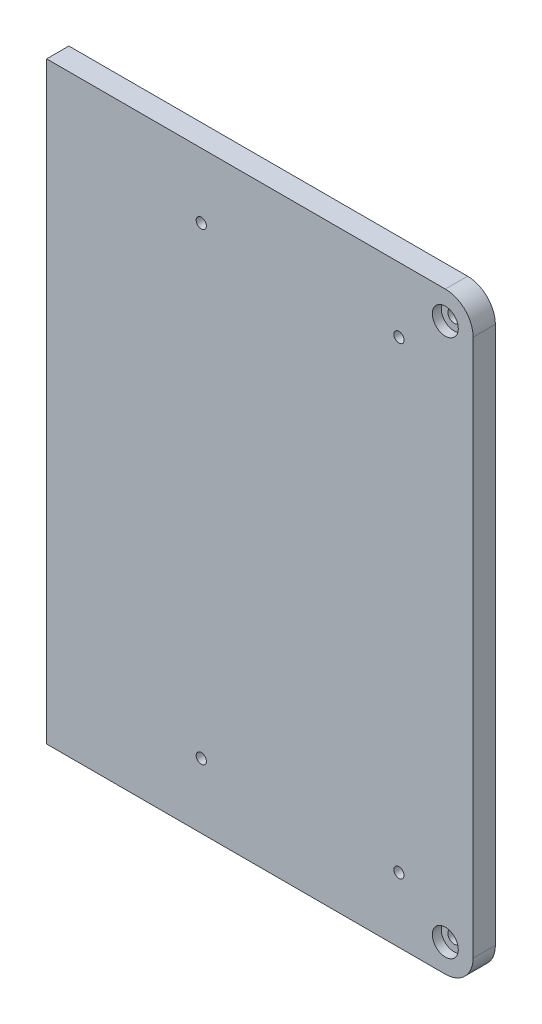
SolidWorks part; units mm, degrees
ref_plane "Front Plane" through (0, 0, 0) normal (0, 0, 1) x (1, 0, 0)
ref_plane "Top Plane" through (0, 0, 0) normal (0, 1, 0) x (1, 0, 0)
ref_plane "Right Plane" through (0, 0, 0) normal (1, 0, 0) x (0, 0, -1)
sketch "Sketch1" plane through (0, 0, 0) normal (0, 0, 1) x (1, 0, 0)
  line L1 (-107.5, 80) -> (107.5, 80)
  line L2 (-115, 72.5) -> (-115, -72.5)
  line L3 (-107.5, -80) -> (107.5, -80)
  line L4 (115, 72.5) -> (115, -72.5)
  line L5 (-115, 80) -> (115, -80) construction
  line L6 (-115, -80) -> (115, 80) construction
  arc A0 (-115, -72.5) -> (-107.5, -80) centre (-107.5, -72.5) ccw
  arc A1 (107.5, -80) -> (115, -72.5) centre (107.5, -72.5) ccw
  arc A2 (107.5, 80) -> (115, 72.5) centre (107.5, 72.5) cw
  arc A3 (-107.5, 80) -> (-115, 72.5) centre (-107.5, 72.5) ccw
  point P0 (0, 0)
  dimension "D3" = 7.5
  dimension "D1" = 230
  dimension "D2" = 160
extrude "Boss-Extrude1" add sketch "Sketch1" along normal blind 6
sketch "Sketch4" plane through (0, 0, 6) normal (0, 0, 1) x (1, 0, 0)
  line L0 (107.5, 80) -> (-107.5, 80) construction
  line L3 (-115, 72.5) -> (-115, -72.5) construction
  line L4 (-107.5, -80) -> (107.5, -80) construction
  circle A0 centre (-96.5, 37.5) radius 1.5
  circle A1 centre (-96.5, -37.5) radius 1.5
  circle A2 centre (-24.5, 37.5) radius 1.5
  circle A3 centre (-24.5, -37.5) radius 1.5
  dimension "D2" = 3
  dimension "D3" = 3
  dimension "D6" = 3
  dimension "D7" = 3
  dimension "D12" = 18.5
  dimension "D1" = 75
  dimension "D4" = 42.5
  dimension "D5" = 18.5
  dimension "D8" = 72
  dimension "D9" = 72
  dimension "D10" = 42.5
  dimension "D11" = 42.5
extrude "Cut-Extrude3" cut sketch "Sketch4" against normal through all
sketch "Sketch5" plane through (0, 0, 6) normal (0, 0, 1) x (1, 0, 0)
  line L0 (-107.5, -80) -> (107.5, -80) construction
  line L1 (107.5, 80) -> (-107.5, 80) construction
  line L2 (115, -72.5) -> (115, 72.5) construction
  circle A0 centre (95, -62.5) radius 1.375
  circle A1 centre (95, 62.5) radius 1.375
  circle A2 centre (41.7, -62.5) radius 1.375
  circle A3 centre (41.7, 62.5) radius 1.375
  dimension "D1" = 125
  dimension "D4" = 2.75
  dimension "D6" = 53.3
  dimension "D7" = 125
  dimension "D8" = 20
  dimension "D9" = 17.5
  dimension "D2" = 17.5
  dimension "D3" = 20
  dimension "D5" = 53.3
extrude "Cut-Extrude4" cut sketch "Sketch5" against normal through all and the other way through all
sketch "Sketch7" plane through (0, 0, 6) normal (0, 0, 1) x (1, 0, 0)
  circle A0 centre (-102.8, 42.3) radius 1.5
  circle A1 centre (-96.5, 37.5) radius 1.5 construction
  circle A2 centre (-102.8, -42.3) radius 1.5
  circle A3 centre (-18.2, -42.3) radius 1.5
  circle A4 centre (-18.2, 42.3) radius 1.5
  circle A5 centre (-96.5, -37.5) radius 1.5 construction
  circle A6 centre (-24.5, -37.5) radius 1.5 construction
  circle A7 centre (-24.5, 37.5) radius 1.5 construction
  dimension "D1" = 6.3
  dimension "D3" = 3
  dimension "D4" = 3
  dimension "D5" = 3
  dimension "D6" = 3
  dimension "D7" = 4.8
  dimension "D8" = 6.3
  dimension "D10" = 4.8
  dimension "D11" = 4.8
  dimension "D12" = 6.3
  dimension "D2" = 4.8
extrude "Cut-Extrude6" cut sketch "Sketch7" against normal through all
sketch "Sketch8" plane through (0, 0, 0) normal (0, 0, -1) x (-1, 0, 0)
  circle A0 centre (18.2, 42.3) radius 3
  circle A1 centre (18.2, -42.3) radius 3
  circle A2 centre (102.8, -42.3) radius 3
  circle A3 centre (102.8, 42.3) radius 3
  dimension "D1" = 6
  dimension "D2" = 6
  dimension "D3" = 6
  dimension "D4" = 6
extrude "Cut-Extrude7" cut sketch "Sketch8" against normal blind 3.5
hole_wizard "CBORE for M3 Pan Head Machine Screw1" positions "Sketch9" profile "Sketch10" counterbore size "M3" standard "ANSI Metric" end condition through all
sketch "Sketch9" plane through (0, 0, 6) normal (0, 0, 1) x (1, 0, 0)
  line L1 (107.5, 80) -> (-107.5, 80) construction
  line L2 (-115, 72.5) -> (-115, -72.5) construction
  line L3 (-107.5, -80) -> (107.5, -80) construction
  line L4 (115, -72.5) -> (115, 72.5) construction
  point P0 (-107.5, 72.5)
  point P2 (-107.5, -72.5)
  point P4 (107.5, -72.5)
  point P6 (107.5, 72.5)
  dimension "D1" = 7.5
  dimension "D2" = 7.5
  dimension "D3" = 7.5
  dimension "D4" = 7.5
  dimension "D5" = 7.5
  dimension "D6" = 7.5
  dimension "D7" = 7.5
  dimension "D8" = 7.5
sketch "Sketch10" plane through (-107.5, 72.5, 6) normal (1, 0, 0) x (0, -1, 0)
  line L0 (0, 0) -> (0, 6)
  line L1 (0, 6) -> (1.7, 6)
  line L3 (1.7, 6) -> (1.7, 2.4)
  line L4 (1.7, 2.4) -> (3.5, 2.4)
  line L5 (3.5, 2.4) -> (3.5, 0)
  line L7 (3.5, 0) -> (0, 0)
  line L11 (0, -6.35) -> (0, 107.95) construction
  dimension "Thru Hole Dia." = 3.4
  dimension "Thru Hole Depth" = 6
  dimension "C'Bore Dia." = 7
  dimension "C'Bore Depth" = 2.4
sketch "Sketch12" plane through (0, 0, 0) normal (0, 0, -1) x (-1, 0, 0)
  line L0 (115, 72.5) -> (115, -72.5) construction
  line L1 (115, 80) -> (0, 80)
  line L2 (115, 80) -> (115, -80)
  line L3 (115, -80) -> (0, -80)
  line L4 (0, 80) -> (0, -80)
  line L5 (107.5, -80) -> (-107.5, -80) construction
  line L6 (-107.5, 80) -> (107.5, 80) construction
  dimension "D1" = 0
  dimension "D2" = 0
  dimension "D3" = 0
  dimension "D4" = 115
extrude "Cut-Extrude8" cut sketch "Sketch12" against normal blind 10
